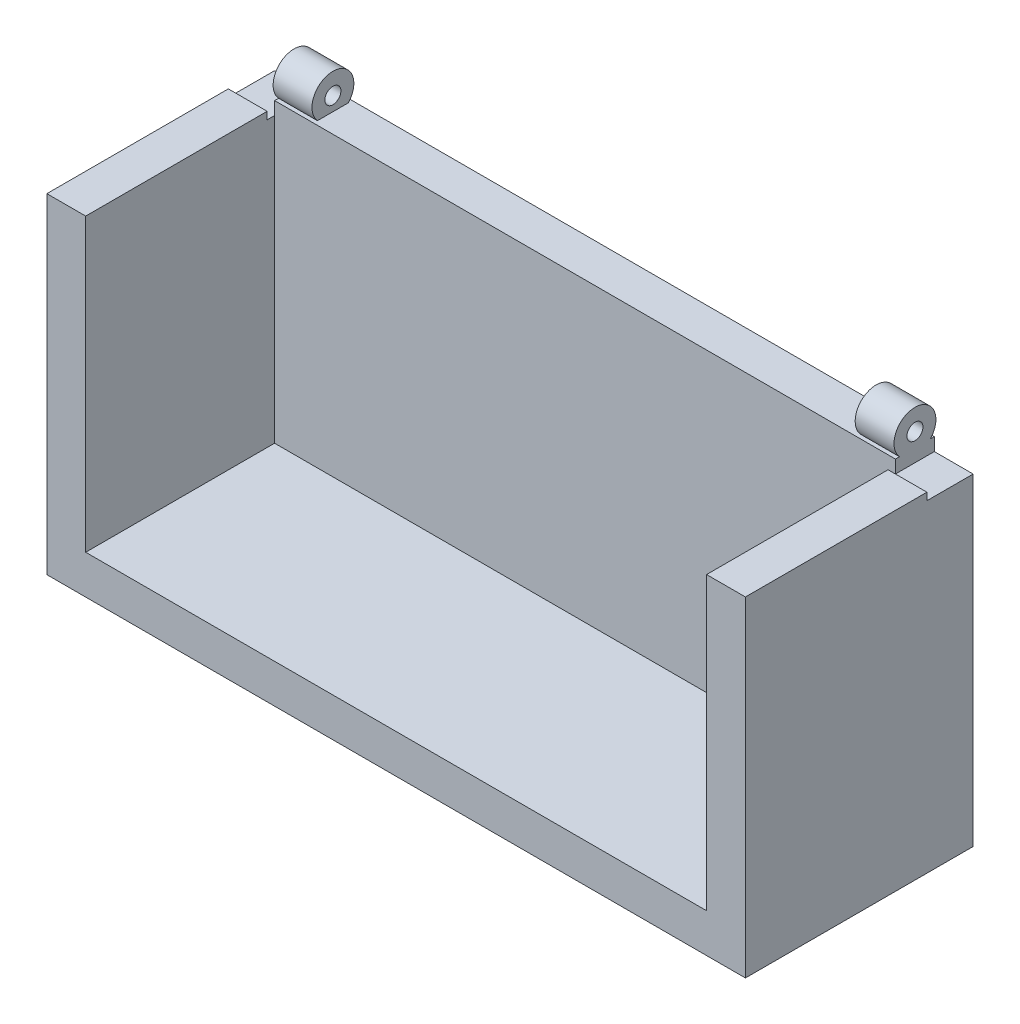
SolidWorks part; units mm, degrees
ref_plane "Front" through (0, 0, 0) normal (0, 0, 1) x (1, 0, 0)
ref_plane "Top" through (0, 0, 0) normal (0, 1, 0) x (1, 0, 0)
ref_plane "Right" through (0, 0, 0) normal (1, 0, 0) x (0, 0, -1)
sketch "Sketch1" plane through (0, 0, 0) normal (0, 1, 0) x (1, 0, 0)
  line L0 (-158.2084, -58.9575) -> (-158.2084, 83.5425)
  line L5 (-158.2084, 83.5425) -> (111.5916, 83.5425)
  line L6 (111.5916, -58.9575) -> (111.5916, 83.5425)
  line L7 (-158.2084, -58.9575) -> (111.5916, -58.9575)
extrude "Boss-Extrude2" add sketch "Sketch1" along normal blind 15
sketch "Sketch2" plane through (0, 15, 0) normal (0, 1, 0) x (1, 0, 0)
  line L8 (-143.2084, -43.9575) -> (96.5916, -43.9575)
  line L9 (96.5916, -43.9575) -> (96.5916, 68.5425)
  line L10 (96.5916, 68.5425) -> (-143.2084, 68.5425)
  line L11 (-143.2084, 68.5425) -> (-143.2084, -43.9575)
  line L12 (-143.2084, -43.9575) -> (96.5916, -43.9575)
  line L13 (96.5916, -43.9575) -> (96.5916, 68.5425)
  line L14 (96.5916, 68.5425) -> (-143.2084, 68.5425)
  line L15 (-143.2084, 68.5425) -> (-143.2084, -43.9575)
  dimension "D1" = 15
extrude "Cut-Extrude1" cut sketch "Sketch2" against normal blind 5
sketch "Sketch3" plane through (0, 15, 0) normal (0, 1, 0) x (1, 0, 0)
  line L0 (-143.2084, 68.5425) -> (-158.2084, 68.5425)
  line L1 (-158.2084, 83.5425) -> (-158.2084, -58.9575) construction
  line L2 (-143.2084, 68.5425) -> (111.5916, 68.5425)
  line L3 (111.5916, -58.9575) -> (111.5916, 83.5425) construction
  line L4 (111.5916, 68.5425) -> (111.5916, 83.5425)
  line L5 (111.5916, 83.5425) -> (-158.2084, 83.5425)
  line L6 (-158.2084, 83.5425) -> (-158.2084, 68.5425)
extrude "Boss-Extrude3" add sketch "Sketch3" along normal blind 75
sketch "Sketch4" plane through (0, 90, 0) normal (0, 1, 0) x (1, 0, 0)
  line L0 (-143.2084, 68.5425) -> (-143.2084, 83.5425) construction
  line L1 (111.5916, 83.5425) -> (-158.2084, 83.5425) construction
  line L2 (-143.2084, 83.5425) -> (-158.2084, 83.5425) construction
  line L3 (-158.2084, 83.5425) -> (-158.2084, 68.5425) construction
  line L4 (-158.2084, 68.5425) -> (-143.2084, 68.5425) construction
  line L5 (111.5916, 68.5425) -> (111.5916, 83.5425) construction
  line L6 (111.5916, 83.5425) -> (96.5916, 83.5425) construction
  line L7 (96.5916, 83.5425) -> (96.5916, 68.5425) construction
  line L8 (96.5916, 68.5425) -> (111.5916, 68.5425) construction
  line L9 (-143.2084, 83.5425) -> (-128.2084, 83.5425) construction
  line L10 (-128.2084, 83.5425) -> (-128.2084, 68.5425) construction
  line L11 (-158.2084, 68.5425) -> (111.5916, 68.5425) construction
  line L12 (-128.2084, 68.5425) -> (-143.2084, 68.5425) construction
  line L13 (96.5916, 83.5425) -> (81.5916, 83.5425) construction
  line L14 (81.5916, 83.5425) -> (81.5916, 68.5425) construction
  line L15 (96.5916, 68.5425) -> (-143.2084, 68.5425) construction
  line L16 (81.5916, 68.5425) -> (96.5916, 68.5425) construction
  dimension "D1" = 15
  dimension "D2" = 15
  dimension "D3" = 15
ref_plane "Plane3" through (-143.2084, 0, 0) normal (1, 0, 0) x (0, 0, -1)
ref_plane "Plane4" through (96.5916, 0, 0) normal (-1, 0, 0) x (0, 0, 1)
sketch "Sketch7" plane through (-143.2084, 0, 0) normal (1, 0, 0) x (0, 0, -1)
  line L0 (84.3883, 95.4538) -> (67.7537, 95.4538) construction
  line L1 (76.071, 86.8252) -> (76.071, 104.0825) construction
  circle A2 centre (76.071, 95.4538) radius 8.0891
  circle A3 centre (76.071, 95.4538) radius 3.0891
  point P9 (76.071, 95.4538)
  dimension "D1" = 5
sketch "Sketch12" plane through (96.5916, 0, 0) normal (-1, 0, 0) x (0, 0, 1)
  line L0 (-76.071, 86.8252) -> (-76.071, 104.0825) construction
  line L1 (-76.071, 86.8252) -> (-76.071, 104.0825)
  circle A0 centre (-76.071, 95.4538) radius 8.0891 construction
  circle A1 centre (-76.071, 95.4538) radius 3.0891 construction
  circle A2 centre (-76.071, 95.4538) radius 8.0891
  circle A3 centre (-76.071, 95.4538) radius 3.0891
sketch "Sketch13" plane through (96.5916, 0, 0) normal (-1, 0, 0) x (0, 0, 1)
  line L0 (-84.3883, 95.4538) -> (-67.7537, 95.4538) construction
  line L1 (-84.3883, 95.4538) -> (-67.7537, 95.4538)
extrude "Boss-Extrude4" add sketch "Sketch7" along normal blind 15
extrude "Boss-Extrude5" add sketch "Sketch12" along normal blind 15 contours A3 L1 A2 | A3 L1 A2
sketch "Sketch15" plane through (0, 90, 0) normal (0, 1, 0) x (1, 0, 0)
  line L0 (-158.2084, 83.5425) -> (-143.2084, 83.5425)
  line L1 (-143.2084, 83.5425) -> (-143.2084, 68.5425)
  line L2 (-143.2084, 68.5425) -> (-158.2084, 68.5425)
  line L3 (-158.2084, 68.5425) -> (-158.2084, 83.5425)
  line L4 (96.5916, 68.5425) -> (111.5916, 68.5425)
  line L5 (111.5916, 68.5425) -> (111.5916, 83.5425)
  line L6 (111.5916, 83.5425) -> (96.5916, 83.5425)
  line L7 (96.5916, 83.5425) -> (96.5916, 68.5425)
extrude "Cut-Extrude2" cut sketch "Sketch15" against normal blind 5
ref_plane "Plane5" through (0, 25, 0) normal (0, 1, 0) x (1, 0, 0)
sketch "Sketch16" plane through (0, 25, 0) normal (0, 1, 0) x (1, 0, 0)
  line L0 (-158.2084, 68.5425) -> (111.5916, 68.5425)
  line L1 (111.5916, 68.5425) -> (111.5916, -58.9575)
  line L2 (111.5916, -58.9575) -> (-158.2084, -58.9575)
  line L3 (-158.2084, -58.9575) -> (-158.2084, 68.5425)
extrude "Cut-Extrude3" cut sketch "Sketch16" against normal blind 49
sketch "Sketch17" plane through (0, 0, 0) normal (0, -1, 0) x (1, 0, 0)
  line L0 (-158.2084, -68.5425) -> (111.5916, -68.5425)
  line L1 (111.5916, -68.5425) -> (111.5916, -83.5425)
  line L2 (111.5916, -83.5425) -> (-158.2084, -83.5425)
  line L3 (-158.2084, -83.5425) -> (-158.2084, -68.5425)
extrude "Boss-Extrude6" add sketch "Sketch17" along normal blind 39.6
sketch "Sketch19" plane through (0, 0, -68.5425) normal (0, 0, 1) x (1, 0, 0)
  line L0 (-158.2084, 85) -> (-158.2084, -39.6)
  line L1 (-158.2084, -39.6) -> (111.5916, -39.6)
  line L2 (111.5916, -39.6) -> (-158.2084, -39.6) construction
  line L3 (111.5916, 85) -> (111.5916, -39.6) construction
  line L4 (111.5916, -39.6) -> (111.5916, 85)
  line L5 (-158.2084, 85) -> (-143.2084, 85)
  line L6 (111.5916, 85) -> (96.5916, 85)
  line L7 (96.5916, 85) -> (96.5916, -24.6)
  line L8 (96.5916, 8.25) -> (96.5916, -8.25) construction
  line L9 (-143.2084, 85) -> (-143.2084, -24.6)
  line L10 (-143.2084, -24.6) -> (96.5916, -24.6)
  dimension "D1" = 15
extrude "Boss-Extrude8" add sketch "Sketch19" along normal blind 72.95 contours L10 L7 L6 L4 L1 L0 L5 L9
sketch "Sketch20" plane through (0, 85, 0) normal (0, 1, 0) x (1, 0, 0)
  line L0 (-158.2084, 65.6823) -> (-143.2084, 65.6823)
  line L1 (-158.2084, 83.5425) -> (-158.2084, -4.4075) construction
  line L2 (-143.2084, -4.4075) -> (-143.2084, 68.5425) construction
  line L3 (-158.2084, -4.4075) -> (-143.2084, -4.4075)
  line L4 (-143.2084, -4.4075) -> (-143.2084, 65.6823)
  line L5 (-158.2084, 65.6823) -> (-158.2084, -4.4075)
  line L6 (-158.2084, 68.5425) -> (-143.2084, 68.5425) construction
  dimension "D1" = 2.8602
sketch "Sketch21" plane through (0, 85, 0) normal (0, 1, 0) x (1, 0, 0)
  line L0 (111.5916, -4.4075) -> (96.5916, -4.4075)
  line L1 (96.5916, -4.4075) -> (96.5916, 65.6823)
  line L2 (96.5916, -4.4075) -> (96.5916, 68.5425) construction
  line L3 (111.5916, -4.4075) -> (111.5916, 65.6823)
  line L4 (111.5916, -4.4075) -> (111.5916, 83.5425) construction
  line L5 (111.5916, 65.6823) -> (96.5916, 65.6823)
  line L6 (96.5916, 68.5425) -> (111.5916, 68.5425) construction
  dimension "D1" = 2.8602
extrude "Boss-Extrude9" add sketch "Sketch20" along normal blind 2.85 contours L4 L0 L5 L3
extrude "Boss-Extrude10" add sketch "Sketch21" along normal blind 2.85 contours L3 L5 L1 L0
